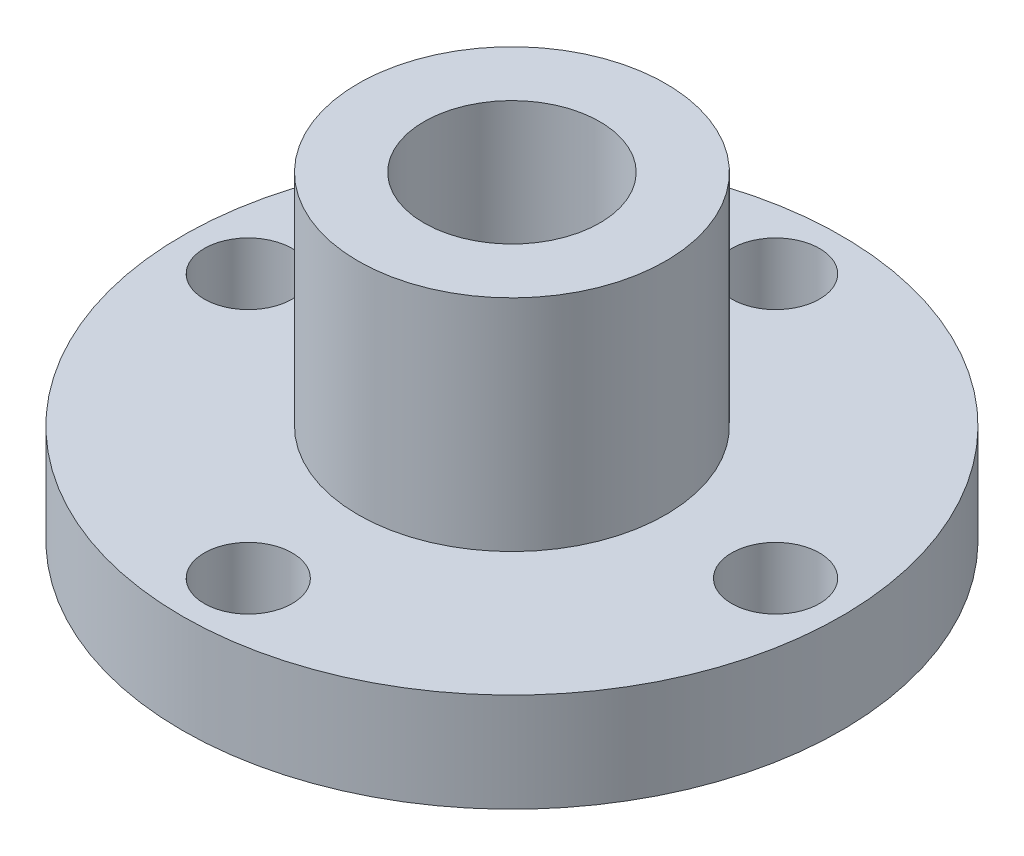
SolidWorks part; units mm, degrees
material "Brass"
ref_plane "Front Plane" through (0, 0, 0) normal (0, 0, 1) x (1, 0, 0)
ref_plane "Top Plane" through (0, 0, 0) normal (0, 1, 0) x (1, 0, 0)
ref_plane "Right Plane" through (0, 0, 0) normal (1, 0, 0) x (0, 0, -1)
sketch "Sketch1" plane through (0, 0, 0) normal (0, 1, 0) x (1, 0, 0)
  circle A0 centre (0, 0) radius 15
  dimension "D1" = 30
extrude "Boss-Extrude1" add sketch "Sketch1" along normal blind 4.5 contours A0
sketch "Sketch3" plane through (0, 4.5, 0) normal (0, 1, 0) x (1, 0, 0)
  circle A0 centre (0, 0) radius 7
  dimension "D1" = 14
extrude "Boss-Extrude2" add sketch "Sketch3" along normal blind 10
sketch "Sketch4" plane through (0, 14.5, 0) normal (0, 1, 0) x (1, 0, 0)
  circle A0 centre (0, 0) radius 4
extrude "Cut-Extrude1" cut sketch "Sketch4" against normal blind 15
sketch "Sketch5" plane through (0, 4.5, 0) normal (0, 1, 0) x (1, 0, 0)
  circle A0 centre (0, 12) radius 2
  circle A1 centre (12, 0) radius 2
  circle A2 centre (0, -12) radius 2
  circle A3 centre (-12, 0) radius 2
  point P12 (0, 0)
  dimension "D1" = 4
  dimension "D2" = 12
  dimension "D3" = 4
extrude "Cut-Extrude2" cut sketch "Sketch5" against normal blind 10
